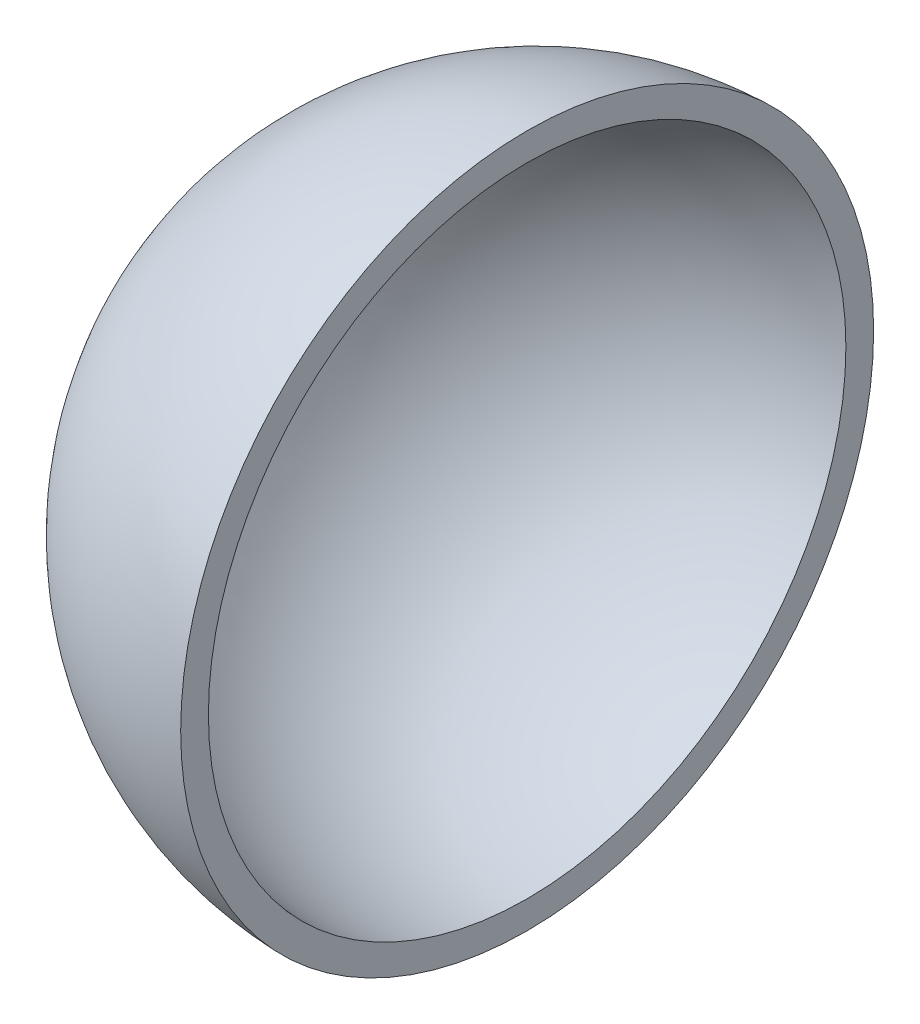
SolidWorks part; units mm, degrees
ref_plane "前视基准面" through (0, 0, 0) normal (0, 0, 1) x (1, 0, 0)
ref_plane "上视基准面" through (0, 0, 0) normal (0, 1, 0) x (1, 0, 0)
ref_plane "右视基准面" through (0, 0, 0) normal (1, 0, 0) x (0, 0, -1)
sketch "草图1" plane through (0, 0, 0) normal (0, 1, 0) x (1, 0, 0)
  line L0 (-37.5, -20.4768) -> (-37.5, 22.9187) construction
  line L1 (-1, 17.2675) -> (-1, -17.1978) construction
  line L2 (0, 0) -> (-24.5737, 0) construction
  line L3 (-34.5, 0) -> (-37.5, 0)
  line L4 (-1, -34.4855) -> (-1, -37.4867)
  arc A0 (-37.5, 0) -> (-1, -37.4867) centre (0, 0) ccw
  arc A1 (-34.5, 0) -> (-1, -34.4855) centre (0, 0) ccw
  circle A2 centre (0, 0) radius 37.5 construction
  circle A3 centre (0, 0) radius 34.5 construction
  dimension "D1" = 75
  dimension "D2" = 36.5
  dimension "D3" = 3
revolve "旋转1" add sketch "草图1" angle 360 about L2
